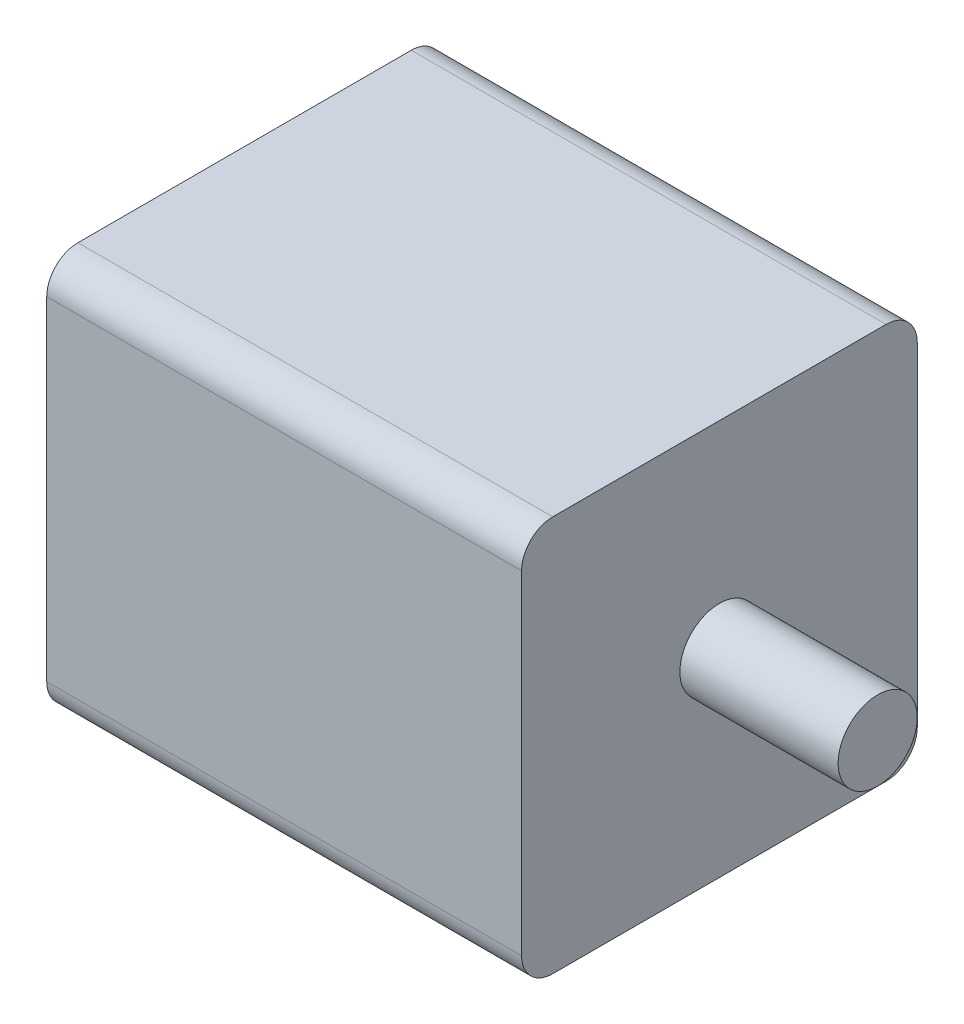
SolidWorks part; units mm, degrees
ref_plane "Front Plane" through (0, 0, 0) normal (0, 0, 1) x (1, 0, 0)
ref_plane "Top Plane" through (0, 0, 0) normal (0, 1, 0) x (1, 0, 0)
ref_plane "Right Plane" through (0, 0, 0) normal (1, 0, 0) x (0, 0, -1)
sketch "Sketch1" plane through (0, 0, 0) normal (1, 0, 0) x (0, 0, -1)
  line L1 (-53.5, 63.5) -> (53.5, 63.5)
  line L2 (-63.5, 53.5) -> (-63.5, -53.5)
  line L3 (-53.5, -63.5) -> (53.5, -63.5)
  line L4 (63.5, 53.5) -> (63.5, -53.5)
  line L5 (-63.5, 63.5) -> (63.5, -63.5) construction
  line L6 (-63.5, -63.5) -> (63.5, 63.5) construction
  arc A0 (-63.5, -53.5) -> (-53.5, -63.5) centre (-53.5, -53.5) ccw
  arc A1 (53.5, -63.5) -> (63.5, -53.5) centre (53.5, -53.5) ccw
  arc A2 (53.5, 63.5) -> (63.5, 53.5) centre (53.5, 53.5) cw
  arc A3 (-53.5, 63.5) -> (-63.5, 53.5) centre (-53.5, 53.5) ccw
  point P0 (0, 0)
  dimension "D3" = 10
  dimension "D1" = 127
  dimension "D2" = 127
extrude "Boss-Extrude1" add sketch "Sketch1" along normal mid plane 152.4
sketch "Sketch2" plane through (76.2, 0, 0) normal (1, 0, 0) x (0, 0, -1)
  circle A0 centre (0, 0) radius 12.7
  dimension "D1" = 25.4
extrude "Boss-Extrude2" add sketch "Sketch2" along normal blind 50.8
